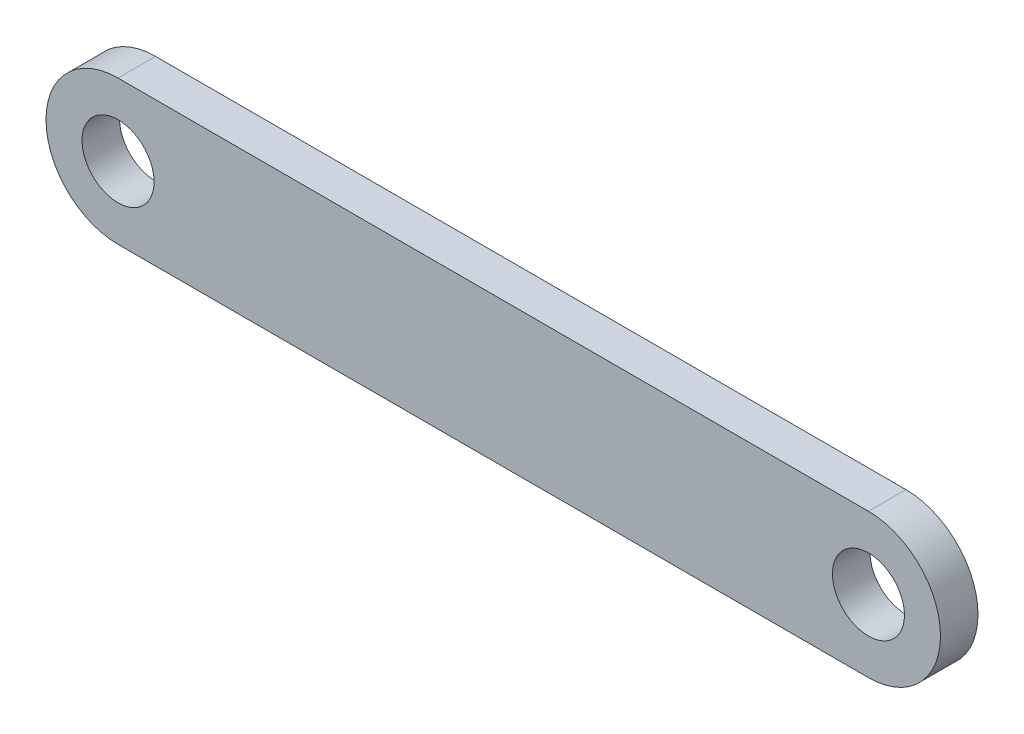
SolidWorks part; units mm, degrees
material "Stainless Steel (ferritic)"
ref_plane "Front Plane" through (0, 0, 0) normal (0, 0, 1) x (1, 0, 0)
ref_plane "Top Plane" through (0, 0, 0) normal (0, 1, 0) x (1, 0, 0)
ref_plane "Right Plane" through (0, 0, 0) normal (1, 0, 0) x (0, 0, -1)
sketch "Sketch1" plane through (0, 0, 0) normal (0, 0, 1) x (1, 0, 0)
  line L0 (0, 12) -> (125, 12)
  line L1 (0, -12) -> (125, -12)
  circle A0 centre (0, 0) radius 6
  arc A1 (0, 12) -> (0, -12) centre (0, 0) ccw
  circle A2 centre (125, 0) radius 6
  arc A3 (125, -12) -> (125, 12) centre (125, 0) ccw
  dimension "D1" = 24
  dimension "D2" = 12
  dimension "D3" = 125
extrude "Boss-Extrude1" add sketch "Sketch1" along normal mid plane 6.25
